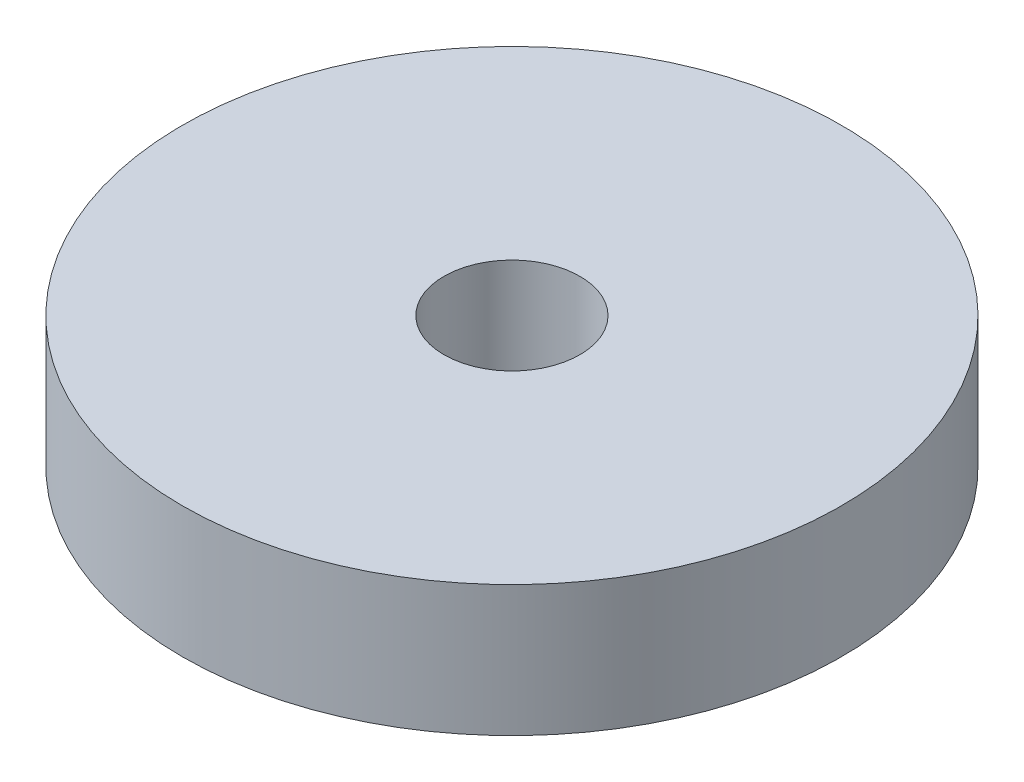
SolidWorks part; units mm, degrees
ref_plane "Front Plane" through (0, 0, 0) normal (0, 0, 1) x (1, 0, 0)
ref_plane "Top Plane" through (0, 0, 0) normal (0, 1, 0) x (1, 0, 0)
ref_plane "Right Plane" through (0, 0, 0) normal (1, 0, 0) x (0, 0, -1)
sketch "Sketch1" plane through (0, 0, 0) normal (0, 1, 0) x (1, 0, 0)
  circle A0 centre (0, 0) radius 8
  circle A1 centre (0, 0) radius 1.65
  dimension "D1" = 16
  dimension "D2" = 3.3
extrude "Boss-Extrude1" add sketch "Sketch1" along normal blind 3.175
